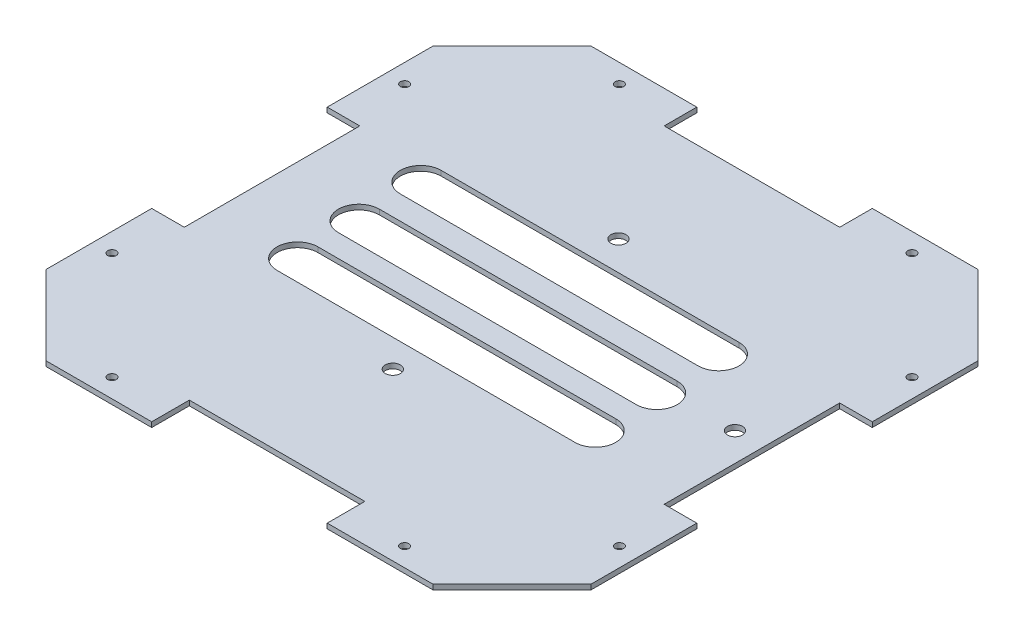
SolidWorks part; units mm, degrees
ref_plane "前视基准面" through (0, 0, 0) normal (0, 0, 1) x (1, 0, 0)
ref_plane "上视基准面" through (0, 0, 0) normal (0, 1, 0) x (1, 0, 0)
ref_plane "右视基准面" through (0, 0, 0) normal (1, 0, 0) x (0, 0, -1)
sketch "草图1" plane through (0, 0, 0) normal (0, 1, 0) x (1, 0, 0)
  line L0 (0, -9.7904) -> (0, 32.3751)
  line L1 (0, 144.5405) -> (31.5269, 176.0674)
  line L2 (31.5269, 176.0674) -> (73.6924, 176.0674)
  line L3 (185.8579, 176.0674) -> (217.3848, 144.5405)
  line L4 (217.3848, 144.5405) -> (217.3848, 102.3751)
  line L5 (217.3848, -9.7904) -> (185.8579, -41.3173)
  line L6 (185.8579, -41.3173) -> (143.6924, -41.3173)
  line L7 (31.5269, -41.3173) -> (0, -9.7904)
  line L8 (31.3198, -41.8173) -> (186.065, -41.8173) construction
  line L9 (73.6924, -41.3173) -> (73.6924, -26.3173)
  line L10 (217.8848, -9.9975) -> (217.8848, 144.7476) construction
  line L11 (-0.5, 144.7476) -> (15.0563, 160.304) construction
  line L12 (186.065, 176.5674) -> (31.3198, 176.5674) construction
  line L13 (186.065, 176.5674) -> (201.6213, 161.0111) construction
  line L14 (201.6213, -26.261) -> (186.065, -41.8173) construction
  line L15 (15.0563, -25.5539) -> (-0.5, -9.9975) construction
  line L16 (-0.5, 144.7476) -> (-0.5, -9.9975) construction
  line L19 (0, 102.3751) -> (13, 102.3751)
  line L28 (73.6924, -26.3173) -> (143.6924, -26.3173)
  line L29 (143.6924, -26.3173) -> (143.6924, -41.3173)
  line L30 (73.6924, -41.3173) -> (31.5269, -41.3173)
  line L31 (13, 102.3751) -> (13, 32.3751)
  line L32 (13, 32.3751) -> (0, 32.3751)
  line L33 (217.3848, 102.3751) -> (204.3848, 102.3751)
  line L34 (204.3848, 102.3751) -> (204.3848, 32.3751)
  line L35 (204.3848, 32.3751) -> (217.3848, 32.3751)
  line L36 (73.6924, 176.0674) -> (73.6924, 163.0674)
  line L37 (73.6924, 163.0674) -> (143.6924, 163.0674)
  line L38 (143.6924, 163.0674) -> (143.6924, 176.0674)
  line L39 (0, 102.3751) -> (0, 144.5405)
  line L40 (217.3848, 32.3751) -> (217.3848, -9.7904)
  line L41 (143.6924, 176.0674) -> (185.8579, 176.0674)
  circle A24 centre (209.8848, 9.0212) radius 1.7
  circle A25 centre (209.8848, 125.7289) radius 1.7
  circle A26 centre (167.0462, 168.5674) radius 1.7
  circle A27 centre (50.3386, 168.5674) radius 1.7
  circle A28 centre (7.5, 125.7289) radius 1.7
  circle A29 centre (7.5, 9.0212) radius 1.7
  circle A30 centre (50.3386, -33.8173) radius 1.7
  circle A31 centre (167.0462, -33.8173) radius 1.7
  point P25 (7.2782, -17.7757)
  dimension "D1" = 0.5
  dimension "D2" = 0.5
  dimension "D3" = 0.5
  dimension "D4" = 0.5
  dimension "D5" = 0.5
  dimension "D6" = 0.5
  dimension "D7" = 0.5
  dimension "D8" = 0.5
  dimension "D9" = 15
  dimension "D10" = 70
  dimension "D11" = 13
  dimension "D12" = 13
  dimension "D13" = 13
  dimension "D14" = 70
  dimension "D15" = 70
  dimension "D16" = 42.1655
  dimension "D17" = 70
  dimension "D18" = 42.1655
extrude "凸台-拉伸1" add sketch "草图1" along normal blind 2
sketch "草图3" plane through (0, 2, 0) normal (0, 1, 0) x (1, 0, 0)
  circle A0 centre (103.6101, 114.9185) radius 3
  circle A1 centre (103.6101, 24.9185) radius 3
  circle A2 centre (193.0689, 71.9185) radius 3
  point P8 (0, 0)
  point P11 (0, 0)
  dimension "D3" = 6
  dimension "D6" = 6
  dimension "D5" = 90
  dimension "D7" = 47
  dimension "D8" = 89.4588
extrude "切除-拉伸1" cut sketch "草图3" against normal blind 10 contours A2 | A1 | A0
sketch "草图4" plane through (0, 2, 0) normal (0, 1, 0) x (1, 0, 0)
  line L0 (44.5618, 95.1037) -> (163.3611, 95.1037) construction
  line L3 (44.5618, 103.2514) -> (163.3611, 103.2514)
  line L6 (44.5618, 86.9559) -> (163.3611, 86.9559)
  line L9 (45.6131, 69.3872) -> (164.4124, 69.3872) construction
  line L10 (45.6131, 77.535) -> (164.4124, 77.535)
  line L11 (45.6131, 61.2395) -> (164.4124, 61.2395)
  line L12 (46.4016, 44.1146) -> (165.2009, 44.1146) construction
  line L13 (46.4016, 52.2623) -> (165.2009, 52.2623)
  line L14 (46.4016, 35.9668) -> (165.2009, 35.9668)
  arc A6 (44.5618, 103.2514) -> (44.5618, 86.9559) centre (44.5618, 95.1037) ccw
  arc A7 (163.3611, 86.9559) -> (163.3611, 103.2514) centre (163.3611, 95.1037) ccw
  arc A8 (45.6131, 77.535) -> (45.6131, 61.2395) centre (45.6131, 69.3872) ccw
  arc A9 (164.4124, 61.2395) -> (164.4124, 77.535) centre (164.4124, 69.3872) ccw
  arc A10 (46.4016, 52.2623) -> (46.4016, 35.9668) centre (46.4016, 44.1146) ccw
  arc A11 (165.2009, 35.9668) -> (165.2009, 52.2623) centre (165.2009, 44.1146) ccw
  point P2 (103.9614, 95.1037)
  point P9 (105.0128, 69.3872)
  point P16 (105.8013, 44.1146)
extrude "切除-拉伸2" cut sketch "草图4" against normal blind 10
